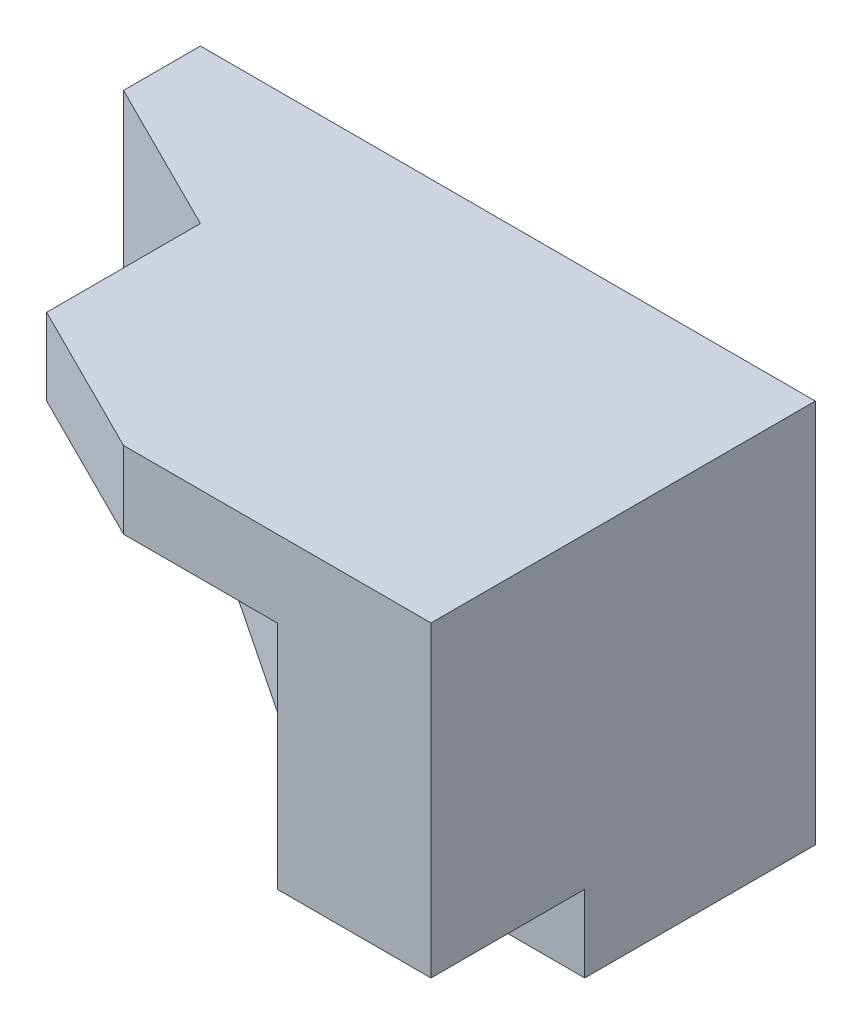
SolidWorks part; units mm, degrees
ref_plane "Front Plane" through (0, 0, 0) normal (0, 0, 1) x (1, 0, 0)
ref_plane "Top Plane" through (0, 0, 0) normal (0, 1, 0) x (1, 0, 0)
ref_plane "Right Plane" through (0, 0, 0) normal (1, 0, 0) x (0, 0, -1)
sketch "Sketch1" plane through (0, 0, 0) normal (0, 0, 1) x (1, 0, 0)
  line L1 (0, 0) -> (80, 0)
  line L2 (0, 0) -> (0, 50)
  line L3 (0, 50) -> (80, 50)
  line L4 (80, 0) -> (80, 50)
  dimension "D1" = 80
  dimension "D2" = 50
extrude "Boss-Extrude1" add sketch "Sketch1" along normal blind 10
sketch "Sketch2" plane through (0, 0, 10) normal (0, 0, 1) x (1, 0, 0)
  line L0 (0, 0) -> (80, 0) construction
  line L1 (60, 0) -> (0, 0)
  line L2 (60, 0) -> (60, 10)
  line L3 (60, 10) -> (0, 10)
  line L4 (0, 0) -> (0, 10)
  line L5 (0, 50) -> (0, 0) construction
  dimension "D1" = 10
  dimension "D2" = 20
extrude "Cut-Extrude1" cut sketch "Sketch2" against normal blind 10
sketch "Sketch3" plane through (0, 0, 10) normal (0, 0, 1) x (1, 0, 0)
  line L0 (40, 10) -> (0, 30)
  line L1 (60, 10) -> (0, 10) construction
  line L2 (0, 50) -> (0, 10) construction
  line L3 (0, 30) -> (0, 10)
  line L4 (0, 10) -> (40, 10)
  dimension "D1" = 20
  dimension "D2" = 20
extrude "Cut-Extrude2" cut sketch "Sketch3" against normal blind 10
sketch "Sketch4" plane through (0, 0, 0) normal (0, -1, 0) x (1, 0, 0)
  line L0 (80, 0) -> (80, 30)
  line L1 (80, 30) -> (70, 30)
  line L2 (70, 30) -> (70, 20)
  line L3 (70, 20) -> (60, 10)
  line L4 (60, 0) -> (80, 0)
  line L5 (60, 10) -> (60, 0)
  dimension "D1" = 30
  dimension "D2" = 10
  dimension "D3" = 10
extrude "Boss-Extrude2" add sketch "Sketch4" against normal blind 10
sketch "Sketch6" plane through (0, 10, 0) normal (0, -1, 0) x (1, 0, 0)
  line L0 (40, 10) -> (80, 10)
  line L1 (80, 10) -> (80, 40)
  line L2 (80, 40) -> (60, 40)
  line L3 (60, 40) -> (40, 30)
  line L4 (40, 30) -> (40, 10)
  dimension "D1" = 30
  dimension "D2" = 20
  dimension "D3" = 20
extrude "Boss-Extrude4" add sketch "Sketch6" against normal blind 40
sketch "Sketch7" plane through (0, 10, 0) normal (0, -1, 0) x (1, 0, 0)
  line L1 (80, 40) -> (60, 40)
  line L2 (80, 40) -> (80, 50)
  line L3 (80, 50) -> (60, 50)
  line L4 (60, 40) -> (60, 50)
  point P5 (80, 40)
  dimension "D1" = 10
  dimension "D2" = 20
extrude "Boss-Extrude5" add sketch "Sketch7" against normal blind 40
sketch "Sketch8" plane through (0, 0, 50) normal (0, 0, 1) x (1, 0, 0)
  line L1 (80, 50) -> (40, 50)
  line L2 (80, 50) -> (80, 40)
  line L3 (80, 40) -> (40, 40)
  line L4 (40, 50) -> (40, 40)
  dimension "D1" = 40
  dimension "D2" = 10
extrude "Boss-Extrude6" add sketch "Sketch8" against normal blind 40
sketch "Sketch9" plane through (0, 40, 0) normal (0, -1, 0) x (-1, 0, 0)
  line L0 (-40, -50) -> (-20, -40)
  line L1 (-20, -40) -> (-20, -23.4135)
  line L2 (-20, -23.4135) -> (-20, -3.4135)
  line L3 (-20, -3.4135) -> (-40, -3.4135)
  line L5 (-40, -50) -> (-40, -3.4135)
  dimension "D1" = 20
  dimension "D2" = 10
  dimension "D3" = 20
  dimension "D4" = 13.4135
extrude "Boss-Extrude7" add sketch "Sketch9" against normal blind 10
ref_plane "Plane1" through (-4, 0, 8) normal (0.4472, 0, -0.8944) x (-0.8944, 0, -0.4472)
sketch "Sketch10" plane through (-4, 0, 8) normal (0.4472, 0, -0.8944) x (-0.8944, 0, -0.4472)
  line L0 (-71.5542, 40) -> (-71.5542, 10)
  line L1 (-71.5542, 10) -> (-4.4721, 30)
  line L2 (-4.4721, 30) -> (-4.4721, 50)
  line L3 (-4.4721, 50) -> (-49.1935, 40)
  line L4 (-49.1935, 40) -> (-71.5542, 40)
extrude "Boss-Extrude8" add sketch "Sketch10" along normal blind 30
sketch "Sketch11" plane through (-4, 0, 8) normal (0.4472, 0, -0.8944) x (-0.8944, 0, -0.4472)
  line L0 (-49.1935, 10) -> (-49.1935, 16.6667)
  line L1 (-49.1935, 16.6667) -> (-4.4721, 30)
  line L2 (-4.4721, 30) -> (-49.1935, 10)
extrude "Boss-Extrude9" add sketch "Sketch11" along normal blind 30
sketch "Sketch13" plane through (12, 24, 0) normal (-0.4472, -0.8944, 0) x (-0.8944, 0.4472, 0)
  line L0 (-31.305, -10) -> (-31.305, -30)
  line L1 (-31.305, -30) -> (13.4164, -10)
  line L2 (13.4164, -10) -> (-31.305, -10)
extrude "Boss-Extrude11" add sketch "Sketch13" against normal blind 20
sketch "Sketch14" plane through (0, 0, 0) normal (0, 0, -1) x (-1, 0, 0)
  line L1 (-80, 50) -> (0, 50)
  line L2 (-80, 50) -> (-80, -7.9263)
  line L3 (-80, -7.9263) -> (0, -7.9263)
  line L4 (0, 50) -> (0, -7.9263)
  dimension "D1" = 80
  dimension "D2" = 57.9263
extrude "Cut-Extrude3" cut sketch "Sketch14" along normal blind 20
sketch "Sketch15" plane through (-4, 0, 8) normal (0.4472, 0, -0.8944) x (-0.8944, 0, -0.4472)
  line L0 (-4.4721, 50) -> (-26.8328, 40)
  line L1 (-26.8328, 40) -> (-26.8328, 50)
  line L2 (-26.8328, 50) -> (-4.4721, 50)
  line L3 (-35.7771, 50) -> (-22.3607, 50) construction
extrude "Boss-Extrude12" add sketch "Sketch15" along normal blind 10
